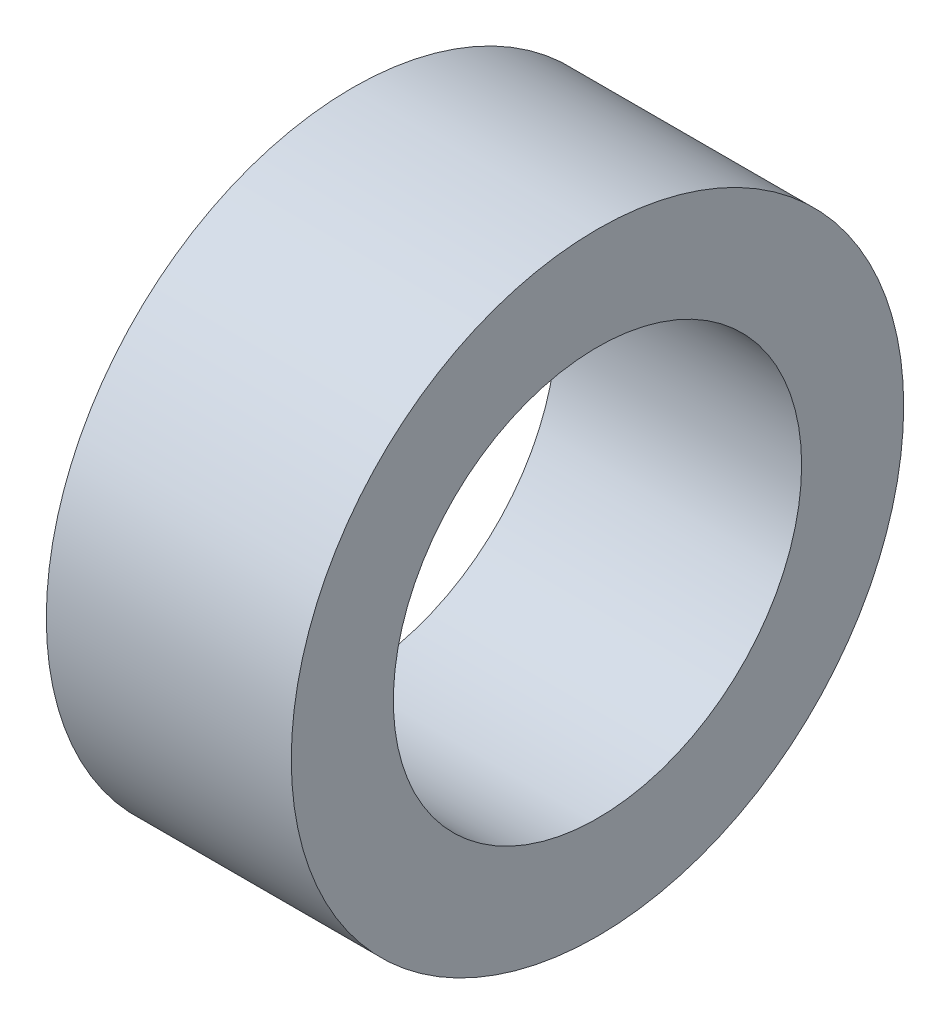
SolidWorks part; units mm, degrees
ref_plane "Front" through (0, 0, 0) normal (0, 0, 1) x (1, 0, 0)
ref_plane "Top" through (0, 0, 0) normal (0, 1, 0) x (1, 0, 0)
ref_plane "Right" through (0, 0, 0) normal (1, 0, 0) x (0, 0, -1)
sketch "草图1" plane through (0, 0, 0) normal (1, 0, 0) x (0, 0, -1)
  circle A0 centre (0, 0) radius 10
  circle A1 centre (0, 0) radius 15
extrude "凸台-拉伸1" add sketch "草图1" along normal blind 12
